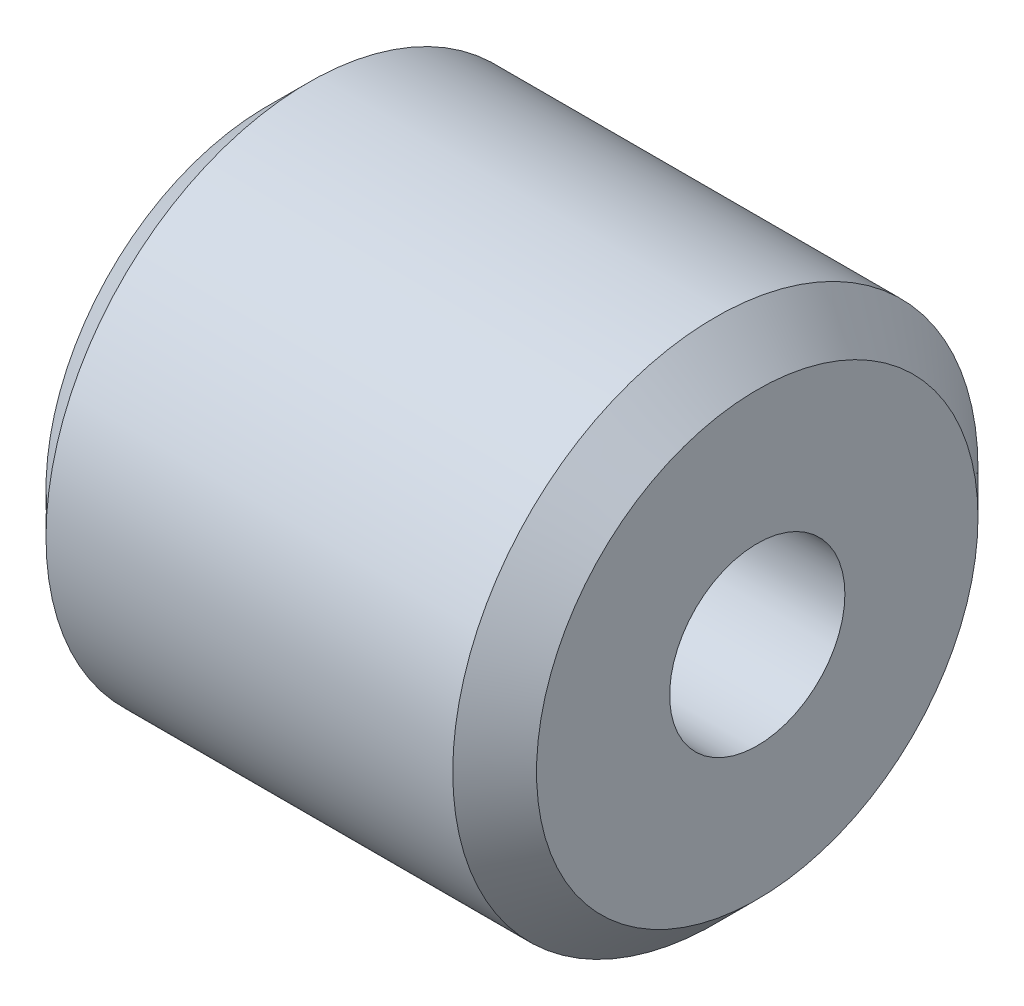
SolidWorks part; units mm, degrees
ref_plane "Front Plane" through (0, 0, 0) normal (0, 0, 1) x (1, 0, 0)
ref_plane "Top Plane" through (0, 0, 0) normal (0, 1, 0) x (1, 0, 0)
ref_plane "Right Plane" through (0, 0, 0) normal (1, 0, 0) x (0, 0, -1)
sketch "Sketch1" plane through (0, 0, 0) normal (1, 0, 0) x (0, 0, -1)
  circle A0 centre (0, 0) radius 1.59
  circle A1 centre (0, 0) radius 4.765
  dimension "D1" = 3.18
  dimension "D2" = 9.53
extrude "Boss-Extrude1" add sketch "Sketch1" along normal mid plane 8.9
chamfer "Chamfer1" distance 0.76 angle 45 2 edges at (-4.45, 0, -4.765) (4.45, 0, -4.765)
